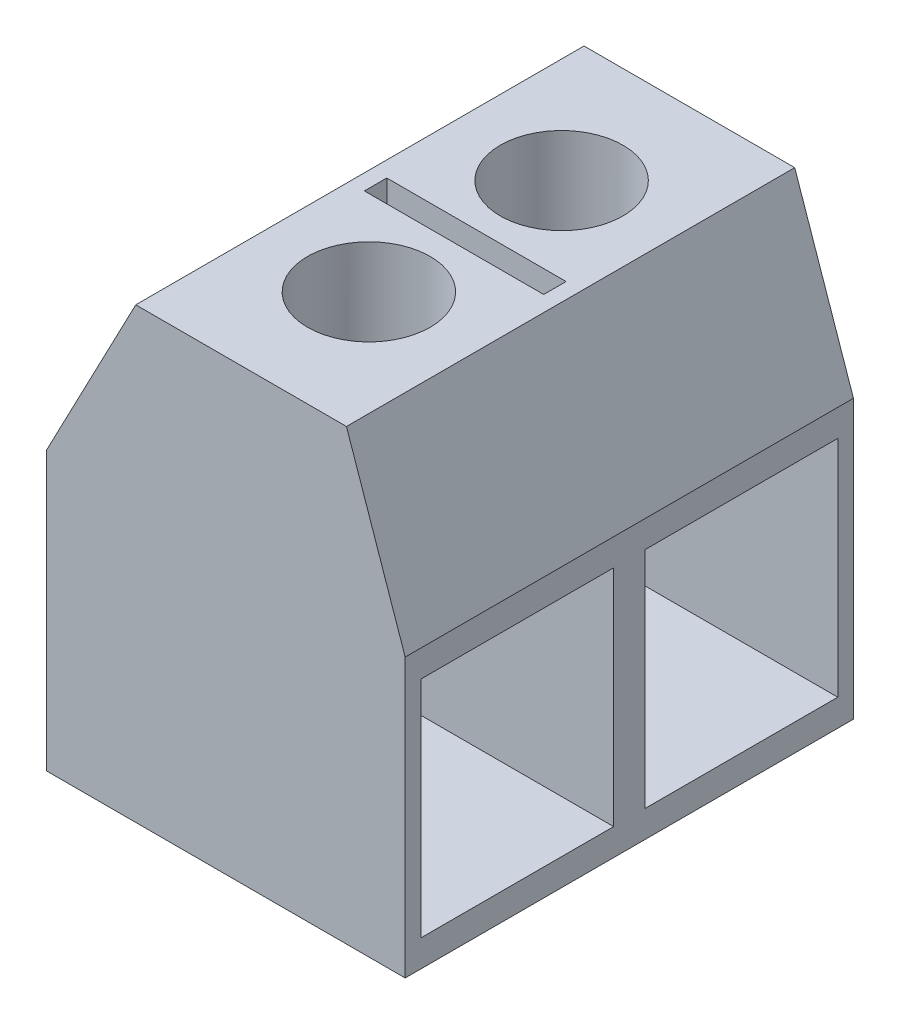
SolidWorks part; units mm, degrees
ref_plane "Front Plane" through (0, 0, 0) normal (0, 0, 1) x (1, 0, 0)
ref_plane "Top Plane" through (0, 0, 0) normal (0, 1, 0) x (1, 0, 0)
ref_plane "Right Plane" through (0, 0, 0) normal (1, 0, 0) x (0, 0, -1)
sketch "Sketch1" plane through (0, 0, 0) normal (0, 0, 1) x (1, 0, 0)
  line L0 (-3.4152, 0) -> (4.5848, 0)
  line L1 (4.5848, 0) -> (4.5848, 6.2)
  line L2 (4.5848, 6.2) -> (3.2747, 10.0006)
  line L3 (3.2747, 10.0006) -> (-1.4253, 10.0006)
  line L4 (-1.4253, 10.0006) -> (-3.4152, 6.2)
  line L5 (-3.4152, 6.2) -> (-3.4152, 0)
  dimension "D1" = 8
  dimension "D2" = 6.2
  dimension "D3" = 6.2
  dimension "D4" = 4.02
  dimension "D5" = 4.29
  dimension "D6" = 4.7
extrude "Boss-Extrude1" add sketch "Sketch1" along normal blind 10
sketch "Sketch2" plane through (4.5848, 0, 0) normal (1, 0, 0) x (0, 0, -1)
  line L0 (-5, 6.2) -> (-5, 0) construction
  line L1 (-10, 6.2) -> (0, 6.2) construction
  line L2 (-10, 0) -> (0, 0) construction
  line L3 (-5, 3.1) -> (0, 3.1) construction
  line L4 (0, 0) -> (0, 6.2) construction
  line L5 (-5.35, 5.6) -> (-9.65, 5.6)
  line L6 (-4.65, 0.6) -> (-0.35, 0.6)
  line L7 (-4.65, 0.6) -> (-4.65, 5.6)
  line L8 (-4.65, 5.6) -> (-0.35, 5.6)
  line L9 (-0.35, 0.6) -> (-0.35, 5.6)
  line L10 (-4.65, 0.6) -> (-0.35, 5.6) construction
  line L11 (-4.65, 5.6) -> (-0.35, 0.6) construction
  line L12 (-9.65, 0.6) -> (-9.65, 5.6)
  line L13 (-5.35, 0.6) -> (-9.65, 0.6)
  line L14 (-5.35, 0.6) -> (-5.35, 5.6)
  point P10 (-2.5, 3.1)
  dimension "D1" = 4.3
  dimension "D2" = 5
extrude "Cut-Extrude1" cut sketch "Sketch2" against normal blind 5.3
sketch "Sketch3" plane through (0, 10.0006, 0) normal (0, 1, 0) x (1, 0, 0)
  line L0 (-1.4253, -5) -> (3.2747, -5) construction
  line L1 (-1.4253, -10) -> (-1.4253, 0) construction
  line L2 (3.2747, -10) -> (3.2747, 0) construction
  line L4 (2.9247, -5.25) -> (-1.0753, -5.25)
  line L5 (2.9247, -5.25) -> (2.9247, -4.75)
  line L6 (2.9247, -4.75) -> (-1.0753, -4.75)
  line L7 (-1.0753, -5.25) -> (-1.0753, -4.75)
  line L8 (2.9247, -5.25) -> (-1.0753, -4.75) construction
  line L9 (2.9247, -4.75) -> (-1.0753, -5.25) construction
  line L10 (0.9247, -2.85) -> (0.9247, -5) construction
  circle A0 centre (0.9247, -2.85) radius 1.3687
  circle A1 centre (0.9247, -7.15) radius 1.3687
  point P6 (0.9247, -5)
  dimension "D1" = 0.5
  dimension "D2" = 4
  dimension "D3" = 2.15
extrude "Cut-Extrude2" cut sketch "Sketch3" against normal blind 5
